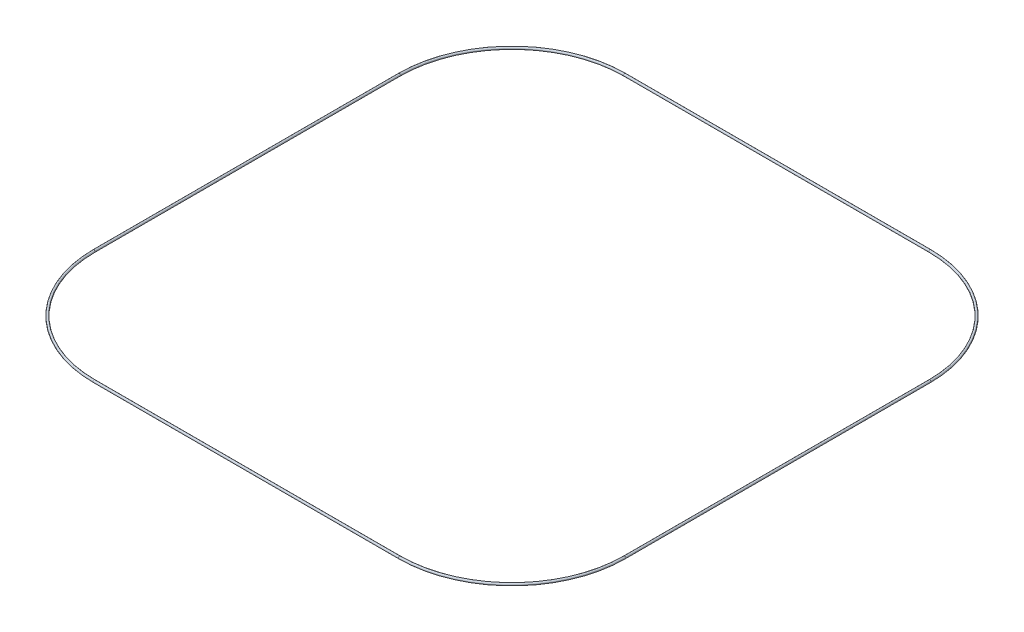
SolidWorks part; units mm, degrees
ref_plane "Front Plane" through (0, 0, 0) normal (0, 0, 1) x (1, 0, 0)
ref_plane "Top Plane" through (0, 0, 0) normal (0, 1, 0) x (1, 0, 0)
ref_plane "Right Plane" through (0, 0, 0) normal (1, 0, 0) x (0, 0, -1)
sketch "Sketch1" plane through (0, 0, 0) normal (0, 1, 0) x (1, 0, 0)
  line L1 (157.48, 0) -> (584.2, 0)
  line L2 (0, 157.48) -> (0, 584.2)
  line L3 (157.48, 741.68) -> (584.2, 741.68)
  line L4 (741.68, 157.48) -> (741.68, 584.2)
  arc A0 (0, 157.48) -> (157.48, 0) centre (157.48, 157.48) ccw
  arc A1 (584.2, 0) -> (741.68, 157.48) centre (584.2, 157.48) ccw
  arc A2 (741.68, 584.2) -> (584.2, 741.68) centre (584.2, 584.2) ccw
  arc A3 (157.48, 741.68) -> (0, 584.2) centre (157.48, 584.2) ccw
  point P5 (0, 0)
  point P6 (0, 0)
  point P9 (0, 0)
  point P13 (741.68, 0)
  point P18 (0, 741.68)
  point P19 (0, 0)
  dimension "D3" = 157.48
  dimension "D1" = 741.68
  dimension "D2" = 741.68
ref_plane "Plane2" through (0, 0, -157.48) normal (0, 0, -1) x (-1, 0, 0)
sketch "Sketch3" plane through (0, 0, -157.48) normal (0, 0, -1) x (-1, 0, 0)
  circle A0 centre (0, 0) radius 1.5875
  dimension "D1" = 3.175
sweep "Sweep2" add profiles "Sketch3" path "Sketch1"
